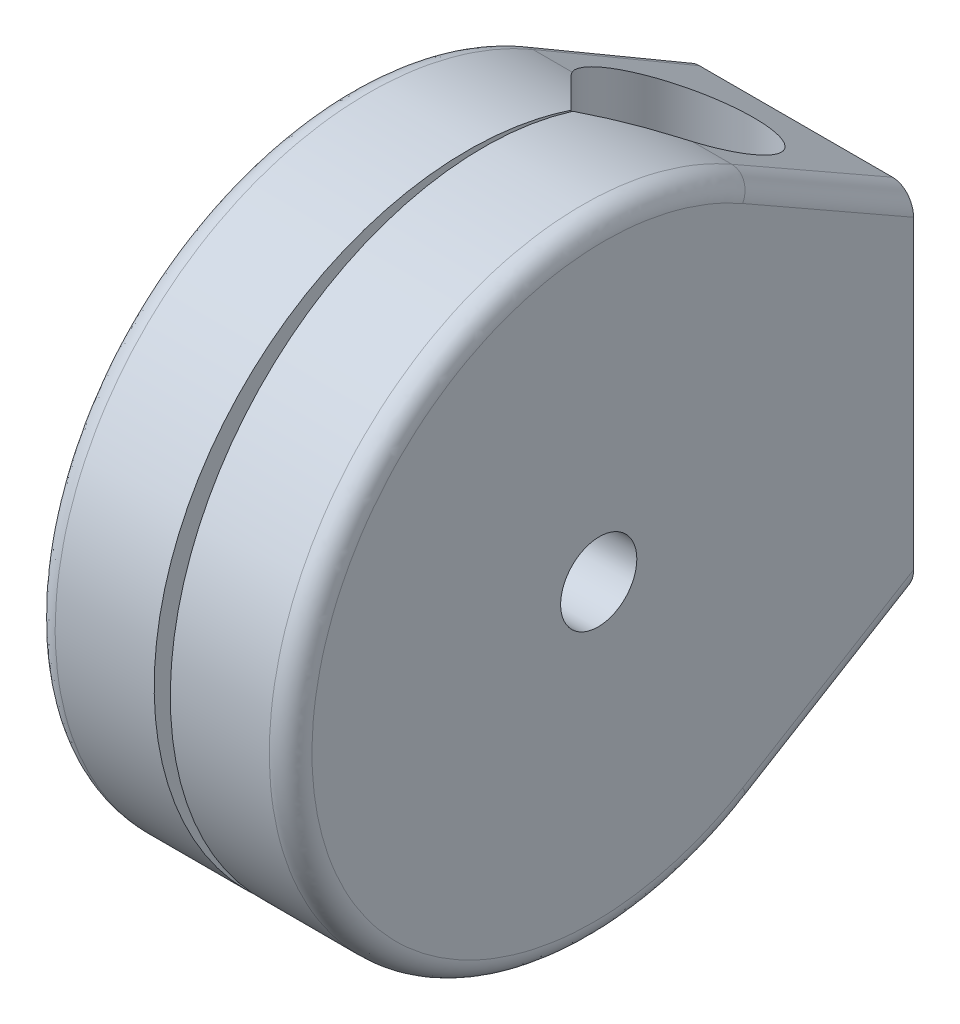
SolidWorks part; units mm, degrees
material "PETG"
ref_plane "Front Plane" through (0, 0, 0) normal (0, 0, 1) x (1, 0, 0)
ref_plane "Top Plane" through (0, 0, 0) normal (0, 1, 0) x (1, 0, 0)
ref_plane "Right Plane" through (0, 0, 0) normal (1, 0, 0) x (0, 0, -1)
sketch "Sketch1" plane through (0, 0, 0) normal (1, 0, 0) x (0, 0, -1)
  line L0 (22.225, 38.4948) -> (45.45, 25.0859)
  line L1 (45.45, 25.0859) -> (45.45, -25.0859)
  line L2 (45.45, -25.0859) -> (22.225, -38.4948)
  line L3 (36.6947, 25.0859) -> (45.45, 25.0859) construction
  circle A0 centre (0, 0) radius 44.45 construction
  arc A1 (22.225, 38.4948) -> (22.225, -38.4948) centre (0, 0) ccw
  point P9 (44.45, 0)
  dimension "D3" = 88.9
  dimension "D1" = 150
  dimension "D2" = 120
  dimension "D4" = 1
extrude "Boss-Extrude1" add sketch "Sketch1" along normal mid plane 33.336
sketch "Sketch2" plane through (0, 0, 0) normal (0, 1, 0) x (1, 0, 0)
  line L0 (-7.5883, 21.1302) -> (0, 28.7185) construction
  line L1 (16.668, 45.45) -> (-16.668, 45.45) construction
  line L2 (0, 28.7185) -> (7.5883, 21.1302) construction
  line L3 (-7.5883, 21.1302) -> (-0.129, 13.6709)
  line L4 (7.5883, 21.1302) -> (0.129, 13.6709)
  line L5 (-0.129, 13.6709) -> (-1.1436, -44.45)
  line L6 (-16.668, -44.45) -> (16.668, -44.45) construction
  line L7 (0.129, 13.6709) -> (1.1436, -44.45)
  line L8 (1.1436, -44.45) -> (-1.1436, -44.45)
  line L9 (-7.5883, 21.1302) -> (0, 13.8022) construction
  line L10 (0, 13.8022) -> (0, -44.45) construction
  line L11 (7.5883, 21.1302) -> (0, 13.8022) construction
  arc A0 (7.5883, 21.1302) -> (-7.5883, 21.1302) centre (0, 28.7185) ccw
  arc A1 (-0.129, 13.6709) -> (0, 13.8022) centre (-7.5883, 21.1302) ccw construction
  point P6 (-10.7315, 28.7185)
  point P8 (0, 39.45)
  point P9 (10.7315, 28.7185)
  dimension "D1" = 10.7315
  dimension "D3" = 90
  dimension "D2" = 6
  dimension "D4" = 2
  dimension "D5" = 1
extrude "Cut-Extrude1" cut sketch "Sketch2" against normal through all both and the other way through all
draft "Draft1" type of draft neutral plane draft angle 1 faces to draft 2 face at (16.668, 0, -17.1688) face at (-16.668, 0, -17.1688) neutral plane through (16.668, 25.0859, -45.45) neutral plane normal (0, 0, -1) parameters "D1"=1
sketch "Sketch3" plane through (17.456, 0, -0.3047) normal (0.9998, 0, -0.0175) x (-0.0175, 0, -0.9998)
  circle A0 centre (-0.3047, 0) radius 5.5
  ellipse E0 centre (-0.3047, 0) end of major axis (44.152, 0) minor radius 44.45 (21.9236, 38.4948) -> (21.9236, -38.4948) ccw construction
  dimension "D1" = 11
extrude "Cut-Extrude2" cut sketch "Sketch3" against normal up to next
sketch "Sketch5" plane through (-17.456, 0, -0.3047) normal (-0.9998, 0, -0.0175) x (-0.0175, 0, 0.9998)
  circle A0 centre (0.3047, 0) radius 5.5
  ellipse E0 centre (0.3047, 0) end of major axis (44.7615, 0) minor radius 44.45 (-21.9236, -38.4948) -> (-21.9236, 38.4948) ccw construction
  dimension "D1" = 11
extrude "Cut-Extrude4" cut sketch "Sketch5" against normal up to next
fillet "Fillet1" radius 3 6 edges at (16.8707, 31.7903, -33.8375) (16.8707, -31.7903, -33.8375) (-16.8707, 31.7903, -33.8375) (-16.8707, -31.7903, -33.8375) (18.2372, 0, 44.45) (-18.2372, 0, 44.45)
